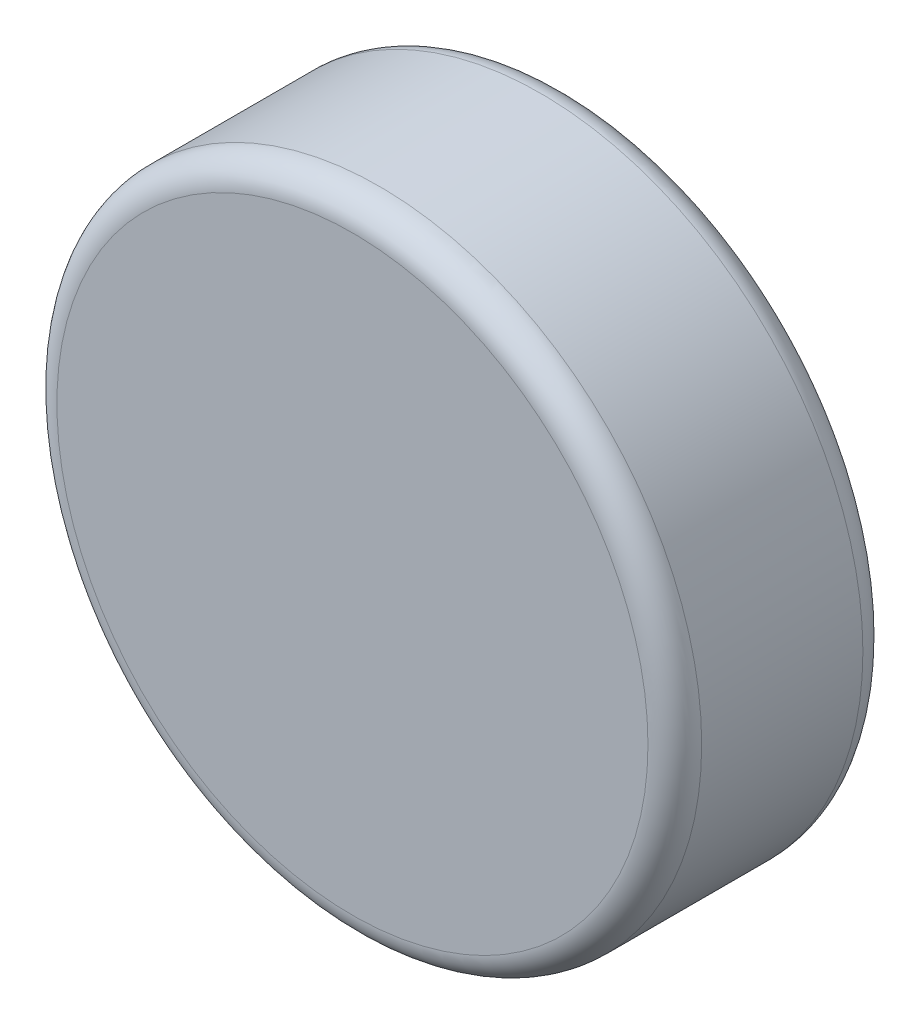
SolidWorks part; units mm, degrees
material "Gray Cast Iron"
ref_plane "Front Plane" through (0, 0, 0) normal (0, 0, 1) x (1, 0, 0)
ref_plane "Top Plane" through (0, 0, 0) normal (0, 1, 0) x (1, 0, 0)
ref_plane "Right Plane" through (0, 0, 0) normal (1, 0, 0) x (0, 0, -1)
sketch "Sketch1" plane through (0, 0, 0) normal (0, 0, 1) x (1, 0, 0)
  circle A0 centre (0, 0) radius 3
  dimension "D1" = 6
extrude "Boss-Extrude1" add sketch "Sketch1" along normal blind 2
fillet "Fillet1" radius 0.25 2 edges at (3, 0, 2) (3, 0, 0)
